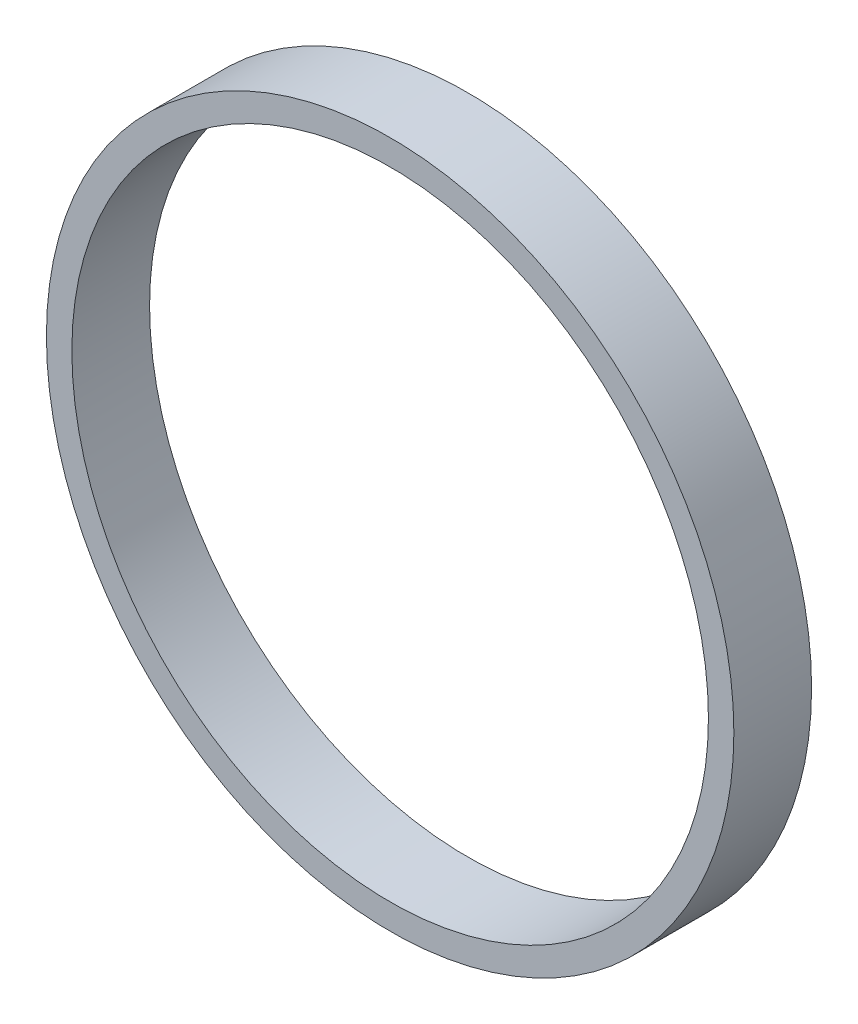
SolidWorks part; units mm, degrees
ref_plane "Front Plane" through (0, 0, 0) normal (0, 0, 1) x (1, 0, 0)
ref_plane "Top Plane" through (0, 0, 0) normal (0, 1, 0) x (1, 0, 0)
ref_plane "Right Plane" through (0, 0, 0) normal (1, 0, 0) x (0, 0, -1)
sketch "Sketch1" plane through (0, 0, 0) normal (0, 0, 1) x (1, 0, 0)
  circle A0 centre (0, 0) radius 22.525
  circle A1 centre (0, 0) radius 24.325
  dimension "D1" = 45.05
  dimension "D2" = 1.8
extrude "Boss-Extrude1" add sketch "Sketch1" along normal blind 5.5
